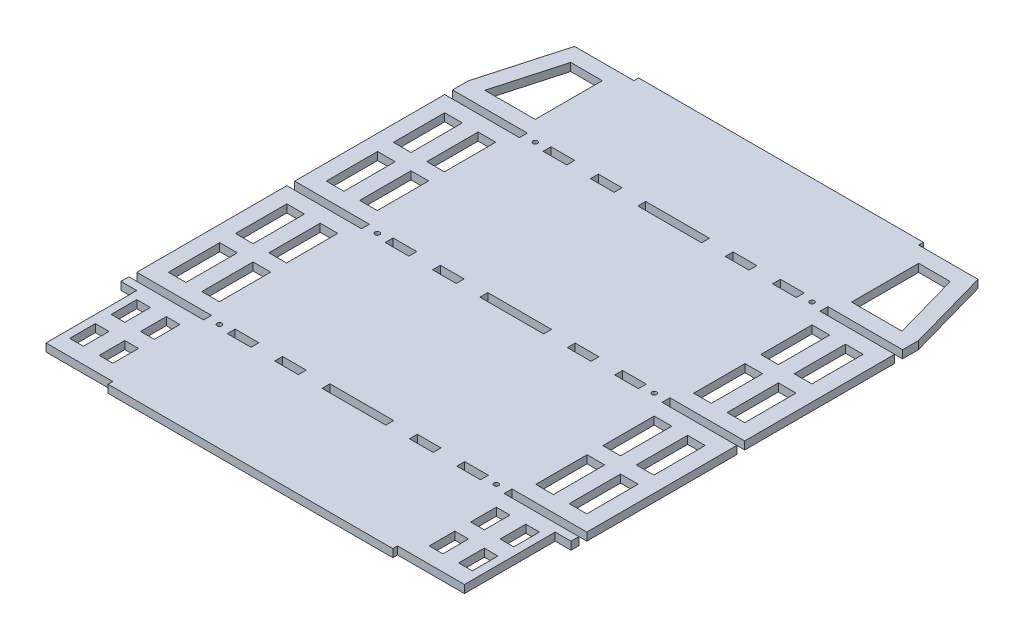
SolidWorks part; units mm, degrees
material "PMMA"
ref_plane "Front Plane" through (0, 0, 0) normal (0, 0, 1) x (1, 0, 0)
ref_plane "Top Plane" through (0, 0, 0) normal (0, 1, 0) x (1, 0, 0)
ref_plane "Right Plane" through (0, 0, 0) normal (1, 0, 0) x (0, 0, -1)
sketch "Schizzo1" plane through (0, 0, 0) normal (0, 1, 0) x (1, 0, 0)
  line L0 (-142.5, 165) -> (142.5, -165) construction
  line L1 (-142.5, 165) -> (142.5, 165)
  line L2 (-142.5, 165) -> (-142.5, -165)
  line L3 (-142.5, -165) -> (142.5, -165)
  line L4 (142.5, 165) -> (142.5, -165)
  point P4 (0, 0)
  dimension "D1" = 330
  dimension "D2" = 285
extrude "Estrusione-Estrusione1" add sketch "Schizzo1" along normal blind 5
sketch "Schizzo3" plane through (0, 0, 0) normal (0, 1, 0) x (1, 0, 0)
  line L0 (-142.5, 0) -> (142.5, 0) construction
  line L1 (-142.5, 165) -> (-142.5, -165) construction
  line L2 (-20.18, -102.5) -> (20.18, -102.5)
  line L3 (0, 165) -> (0, -165) construction
  line L4 (142.5, 165) -> (-142.5, 165) construction
  line L5 (-142.5, -165) -> (142.5, -165) construction
  line L6 (-50.18, -2.5) -> (-35.18, -2.5)
  line L7 (-80.18, 2.5) -> (-65.18, 2.5)
  line L8 (-80.18, 2.5) -> (-80.18, -2.5)
  line L9 (-80.18, -2.5) -> (-65.18, -2.5)
  line L10 (-65.18, 2.5) -> (-65.18, -2.5)
  line L11 (-35.18, 2.5) -> (-35.18, -2.5)
  line L12 (-50.18, 2.5) -> (-35.18, 2.5)
  line L13 (-50.18, 2.5) -> (-50.18, -2.5)
  line L14 (80.18, 2.5) -> (80.18, -2.5)
  line L15 (80.18, 2.5) -> (65.18, 2.5)
  line L16 (65.18, 2.5) -> (65.18, -2.5)
  line L17 (80.18, -2.5) -> (65.18, -2.5)
  line L18 (50.18, 2.5) -> (50.18, -2.5)
  line L19 (50.18, 2.5) -> (35.18, 2.5)
  line L20 (35.18, 2.5) -> (35.18, -2.5)
  line L21 (50.18, -2.5) -> (35.18, -2.5)
  line L22 (-80.18, 97.5) -> (-65.18, 97.5)
  line L23 (-65.18, 102.5) -> (-65.18, 97.5)
  line L24 (-80.18, 102.5) -> (-65.18, 102.5)
  line L25 (-80.18, 102.5) -> (-80.18, 97.5)
  line L26 (-50.18, 97.5) -> (-35.18, 97.5)
  line L27 (-35.18, 102.5) -> (-35.18, 97.5)
  line L28 (-50.18, 102.5) -> (-35.18, 102.5)
  line L29 (-50.18, 102.5) -> (-50.18, 97.5)
  line L30 (-80.18, -102.5) -> (-65.18, -102.5)
  line L31 (-65.18, -97.5) -> (-65.18, -102.5)
  line L32 (-80.18, -97.5) -> (-65.18, -97.5)
  line L33 (-80.18, -97.5) -> (-80.18, -102.5)
  line L34 (-50.18, -102.5) -> (-35.18, -102.5)
  line L35 (-35.18, -97.5) -> (-35.18, -102.5)
  line L36 (-50.18, -97.5) -> (-35.18, -97.5)
  line L37 (-50.18, -97.5) -> (-50.18, -102.5)
  line L38 (50.18, 102.5) -> (50.18, 97.5)
  line L39 (50.18, 102.5) -> (35.18, 102.5)
  line L40 (35.18, 102.5) -> (35.18, 97.5)
  line L41 (50.18, 97.5) -> (35.18, 97.5)
  line L42 (80.18, 102.5) -> (80.18, 97.5)
  line L43 (80.18, 102.5) -> (65.18, 102.5)
  line L44 (65.18, 102.5) -> (65.18, 97.5)
  line L45 (80.18, 97.5) -> (65.18, 97.5)
  line L46 (50.18, -97.5) -> (50.18, -102.5)
  line L47 (50.18, -97.5) -> (35.18, -97.5)
  line L48 (35.18, -97.5) -> (35.18, -102.5)
  line L49 (50.18, -102.5) -> (35.18, -102.5)
  line L50 (80.18, -97.5) -> (80.18, -102.5)
  line L51 (80.18, -97.5) -> (65.18, -97.5)
  line L52 (65.18, -97.5) -> (65.18, -102.5)
  line L53 (80.18, -102.5) -> (65.18, -102.5)
  line L54 (142.5, -165) -> (142.5, 165) construction
  line L55 (-142.5, 97.5) -> (-95.18, 97.5)
  line L56 (-20.18, 2.5) -> (20.18, 2.5)
  line L57 (-20.18, 2.5) -> (-20.18, -2.5)
  line L58 (-20.18, -2.5) -> (20.18, -2.5)
  line L59 (20.18, 2.5) -> (20.18, -2.5)
  line L60 (20.18, -97.5) -> (20.18, -102.5)
  line L61 (-20.18, -97.5) -> (20.18, -97.5)
  line L62 (-20.18, -97.5) -> (-20.18, -102.5)
  line L63 (0, 65) -> (0, -265) construction
  line L64 (-20.18, 97.5) -> (20.18, 97.5)
  line L65 (20.18, 102.5) -> (20.18, 97.5)
  line L66 (-20.18, 102.5) -> (20.18, 102.5)
  line L67 (-20.18, 102.5) -> (-20.18, 97.5)
  line L68 (-142.5, 2.5) -> (-95.18, 2.5)
  line L69 (-142.5, 2.5) -> (-142.5, -2.5)
  line L70 (-142.5, -2.5) -> (-95.18, -2.5)
  line L71 (-95.18, 2.5) -> (-95.18, -2.5)
  line L72 (-95.18, 102.5) -> (-95.18, 97.5)
  line L73 (-142.5, 102.5) -> (-95.18, 102.5)
  line L74 (-142.5, 102.5) -> (-142.5, 97.5)
  line L75 (-142.5, -97.5) -> (-95.18, -97.5)
  line L76 (-95.18, -97.5) -> (-95.18, -102.5)
  line L77 (-142.5, -102.5) -> (-95.18, -102.5)
  line L78 (-142.5, -97.5) -> (-142.5, -102.5)
  line L79 (142.5, -97.5) -> (142.5, -102.5)
  line L80 (142.5, -102.5) -> (95.18, -102.5)
  line L81 (95.18, -97.5) -> (95.18, -102.5)
  line L82 (142.5, -97.5) -> (95.18, -97.5)
  line L83 (142.5, 102.5) -> (142.5, 97.5)
  line L84 (142.5, 102.5) -> (95.18, 102.5)
  line L85 (95.18, 102.5) -> (95.18, 97.5)
  line L86 (142.5, 97.5) -> (95.18, 97.5)
  line L87 (142.5, 2.5) -> (142.5, -2.5)
  line L88 (142.5, 2.5) -> (95.18, 2.5)
  line L89 (95.18, 2.5) -> (95.18, -2.5)
  line L90 (142.5, -2.5) -> (95.18, -2.5)
  circle A0 centre (-87.68, 0) radius 1.5
  circle A1 centre (87.68, 0) radius 1.5
  circle A2 centre (-87.68, 100) radius 1.5
  circle A3 centre (-87.68, -100) radius 1.5
  circle A4 centre (87.68, -100) radius 1.5
  circle A5 centre (87.68, 100) radius 1.5
  circle A8 centre (-5.0427, -204.0432) radius 1.5
  point P81 (-20.18, 0)
  point P82 (0, 2.5)
  point P84 (-65.18, 0)
  point P96 (-142.5, 0)
  dimension "D7" = 3
  dimension "D1" = 15
  dimension "D3" = 5
  dimension "D10" = 5
  dimension "D11" = 40.36
  dimension "D14" = 7.5
  dimension "D16" = 47.32
  dimension "D2" = 62.32
  dimension "D15" = 107.32
  dimension "D4" = 2
  dimension "D5" = 2
  dimension "D6" = 2
  dimension "D8" = 2
  dimension "D9" = 2
  dimension "D12" = 2
  dimension "D13" = 2
  dimension "D17" = 2
  dimension "D18" = 2
extrude "Taglio-Estrusione1" cut sketch "Schizzo3" along direction (0, 1, 0) on the side of the normal through all
sketch "Schizzo4" plane through (0, 0, 165) normal (0, 0, 1) x (1, 0, 0)
  line L0 (-142.5, 5) -> (142.5, 5) construction
  line L1 (-90.17, 5) -> (90.17, 5)
  line L2 (-90.17, 5) -> (-90.17, 0)
  line L3 (-90.17, 0) -> (90.17, 0)
  line L4 (90.17, 5) -> (90.17, 0)
  line L5 (-142.5, 0) -> (142.5, 0) construction
  line L6 (-142.5, 5) -> (-142.5, 0) construction
  point P4 (0, 5)
  point P7 (0, 5)
  point P10 (-142.5, 2.5)
  dimension "D1" = 52.33
extrude "Estrusione-Estrusione2" add sketch "Schizzo4" along normal blind 3
sketch "Schizzo5" plane through (0, 0, -165) normal (0, 0, -1) x (-1, 0, 0)
  line L0 (-142.5, 5) -> (142.5, 5) construction
  line L1 (-90.18, 5) -> (90.18, 5)
  line L2 (-90.18, 5) -> (-90.18, 0)
  line L3 (-90.18, 0) -> (90.18, 0)
  line L4 (90.18, 5) -> (90.18, 0)
  line L5 (-142.5, 0) -> (142.5, 0) construction
  line L6 (-142.5, 5) -> (-142.5, 0) construction
  point P4 (0, 5)
  point P7 (0, 5)
  dimension "D1" = 52.32
extrude "Estrusione-Estrusione3" add sketch "Schizzo5" along normal blind 3
sketch "Schizzo6" plane through (0, 0, 0) normal (0, 1, 0) x (1, 0, 0)
  line L0 (-142.5, 165) -> (-127.7589, 165)
  line L1 (-90.18, 165) -> (-142.5, 165) construction
  line L2 (-127.7589, 165) -> (-142.5, 112.5)
  line L3 (-142.5, 165) -> (-142.5, 102.5) construction
  line L4 (-142.5, 112.5) -> (-142.5, 165)
  line L5 (-95.18, 102.5) -> (-142.5, 102.5) construction
  line L6 (-132.1133, 112.5) -> (-100.18, 112.5)
  line L7 (-100.18, 112.5) -> (-100.18, 155)
  line L8 (-100.18, 155) -> (-120.18, 155)
  line L9 (-120.18, 155) -> (-132.1133, 112.5)
  line L10 (108.84, -138.75) -> (108.84, -155)
  line L11 (108.84, -155) -> (100.18, -155)
  line L12 (100.18, -138.75) -> (100.18, -155)
  line L13 (108.84, -138.75) -> (100.18, -138.75)
  line L14 (-95.18, 97.5) -> (-95.18, 102.5) construction
  line L15 (-90.18, 168) -> (-90.18, 165) construction
  line L16 (0, 168) -> (0, -168) construction
  line L17 (-90.18, 168) -> (90.18, 168) construction
  line L18 (90.17, -168) -> (-90.17, -168) construction
  line L19 (132.1133, 112.5) -> (100.18, 112.5)
  line L20 (120.18, 155) -> (132.1133, 112.5)
  line L21 (100.18, 155) -> (120.18, 155)
  line L22 (100.18, 112.5) -> (100.18, 155)
  line L23 (142.5, 165) -> (127.7589, 165)
  line L24 (142.5, 112.5) -> (142.5, 165)
  line L25 (127.7589, 165) -> (142.5, 112.5)
  line L26 (-142.5, -102.5) -> (-95.18, -102.5) construction
  line L27 (-127.5, -112.5) -> (-118.84, -112.5)
  line L28 (-127.5, -112.5) -> (-127.5, -128.75)
  line L29 (-127.5, -128.75) -> (-118.84, -128.75)
  line L30 (-118.84, -112.5) -> (-118.84, -128.75)
  line L31 (-142.5, -102.5) -> (-142.5, -165) construction
  line L32 (-108.84, -112.5) -> (-100.18, -112.5)
  line L33 (-108.84, -112.5) -> (-108.84, -128.75)
  line L34 (-108.84, -128.75) -> (-100.18, -128.75)
  line L35 (-100.18, -112.5) -> (-100.18, -128.75)
  line L36 (-95.18, -102.5) -> (-95.18, -97.5) construction
  line L37 (-127.5, -138.75) -> (-118.84, -138.75)
  line L38 (-127.5, -138.75) -> (-127.5, -155)
  line L39 (-127.5, -155) -> (-118.84, -155)
  line L40 (-118.84, -138.75) -> (-118.84, -155)
  line L41 (-108.84, -138.75) -> (-100.18, -138.75)
  line L42 (-108.84, -138.75) -> (-108.84, -155)
  line L43 (-108.84, -155) -> (-100.18, -155)
  line L44 (-100.18, -138.75) -> (-100.18, -155)
  line L45 (-142.5, -165) -> (-90.17, -165) construction
  line L46 (127.5, -138.75) -> (127.5, -155)
  line L47 (127.5, -155) -> (118.84, -155)
  line L48 (118.84, -138.75) -> (118.84, -155)
  line L49 (127.5, -138.75) -> (118.84, -138.75)
  line L50 (108.84, -112.5) -> (108.84, -128.75)
  line L51 (108.84, -112.5) -> (100.18, -112.5)
  line L52 (100.18, -112.5) -> (100.18, -128.75)
  line L53 (108.84, -128.75) -> (100.18, -128.75)
  line L54 (127.5, -112.5) -> (127.5, -128.75)
  line L55 (127.5, -112.5) -> (118.84, -112.5)
  line L56 (118.84, -112.5) -> (118.84, -128.75)
  line L57 (127.5, -128.75) -> (118.84, -128.75)
  line L58 (-132.5, -12.5) -> (-121.34, -12.5)
  line L59 (-132.5, -12.5) -> (-132.5, -45)
  line L60 (-132.5, -45) -> (-121.34, -45)
  line L61 (-121.34, -12.5) -> (-121.34, -45)
  line L62 (-111.34, -12.5) -> (-100.18, -12.5)
  line L63 (-111.34, -12.5) -> (-111.34, -45)
  line L64 (-111.34, -45) -> (-100.18, -45)
  line L65 (-100.18, -12.5) -> (-100.18, -45)
  line L66 (-132.5, -55) -> (-121.34, -55)
  line L67 (-132.5, -55) -> (-132.5, -87.5)
  line L68 (-132.5, -87.5) -> (-121.34, -87.5)
  line L69 (-121.34, -55) -> (-121.34, -87.5)
  line L70 (-111.34, -55) -> (-100.18, -55)
  line L71 (-111.34, -55) -> (-111.34, -87.5)
  line L72 (-111.34, -87.5) -> (-100.18, -87.5)
  line L73 (-100.18, -55) -> (-100.18, -87.5)
  line L74 (-142.5, -2.5) -> (-142.5, -97.5) construction
  line L75 (-142.5, -2.5) -> (-95.18, -2.5) construction
  line L76 (-95.18, -2.5) -> (-95.18, 2.5) construction
  line L77 (-95.18, -97.5) -> (-142.5, -97.5) construction
  line L78 (111.34, -55) -> (100.18, -55)
  line L79 (111.34, -55) -> (111.34, -87.5)
  line L80 (111.34, -87.5) -> (100.18, -87.5)
  line L81 (100.18, -55) -> (100.18, -87.5)
  line L82 (132.5, -55) -> (121.34, -55)
  line L83 (132.5, -55) -> (132.5, -87.5)
  line L84 (132.5, -87.5) -> (121.34, -87.5)
  line L85 (121.34, -55) -> (121.34, -87.5)
  line L86 (111.34, -12.5) -> (100.18, -12.5)
  line L87 (111.34, -12.5) -> (111.34, -45)
  line L88 (111.34, -45) -> (100.18, -45)
  line L89 (100.18, -12.5) -> (100.18, -45)
  line L90 (132.5, -12.5) -> (121.34, -12.5)
  line L91 (132.5, -12.5) -> (132.5, -45)
  line L92 (132.5, -45) -> (121.34, -45)
  line L93 (121.34, -12.5) -> (121.34, -45)
  line L94 (-95.18, 0) -> (95.18, 0) construction
  line L95 (95.18, 2.5) -> (95.18, -2.5) construction
  line L96 (111.34, 55) -> (100.18, 55)
  line L97 (100.18, 55) -> (100.18, 87.5)
  line L98 (111.34, 87.5) -> (100.18, 87.5)
  line L99 (111.34, 55) -> (111.34, 87.5)
  line L100 (132.5, 55) -> (121.34, 55)
  line L101 (121.34, 55) -> (121.34, 87.5)
  line L102 (132.5, 87.5) -> (121.34, 87.5)
  line L103 (132.5, 55) -> (132.5, 87.5)
  line L104 (132.5, 12.5) -> (121.34, 12.5)
  line L105 (121.34, 12.5) -> (121.34, 45)
  line L106 (132.5, 45) -> (121.34, 45)
  line L107 (132.5, 12.5) -> (132.5, 45)
  line L108 (111.34, 12.5) -> (100.18, 12.5)
  line L109 (111.34, 12.5) -> (111.34, 45)
  line L110 (111.34, 45) -> (100.18, 45)
  line L111 (100.18, 12.5) -> (100.18, 45)
  line L112 (-132.5, 55) -> (-121.34, 55)
  line L113 (-132.5, 55) -> (-132.5, 87.5)
  line L114 (-132.5, 87.5) -> (-121.34, 87.5)
  line L115 (-121.34, 55) -> (-121.34, 87.5)
  line L116 (-111.34, 55) -> (-100.18, 55)
  line L117 (-111.34, 55) -> (-111.34, 87.5)
  line L118 (-111.34, 87.5) -> (-100.18, 87.5)
  line L119 (-100.18, 55) -> (-100.18, 87.5)
  line L120 (-111.34, 12.5) -> (-100.18, 12.5)
  line L121 (-111.34, 12.5) -> (-111.34, 45)
  line L122 (-111.34, 45) -> (-100.18, 45)
  line L123 (-100.18, 12.5) -> (-100.18, 45)
  line L124 (-132.5, 12.5) -> (-121.34, 12.5)
  line L125 (-132.5, 12.5) -> (-132.5, 45)
  line L126 (-132.5, 45) -> (-121.34, 45)
  line L127 (-121.34, 12.5) -> (-121.34, 45)
  line L128 (142.5, -107.5) -> (132.5, -107.5)
  line L129 (-142.5, -107.5) -> (-132.5, -107.5)
  line L130 (-142.5, -107.5) -> (-142.5, -165)
  line L131 (-142.5, -165) -> (-132.5, -165)
  line L132 (-132.5, -107.5) -> (-132.5, -165)
  line L133 (142.5, -107.5) -> (142.5, -165)
  line L134 (142.5, -165) -> (132.5, -165)
  line L135 (132.5, -107.5) -> (132.5, -165)
  point P13 (-95.18, 100)
  point P45 (-95.18, -100)
  dimension "D1" = 10
  dimension "D2" = 5
  dimension "D3" = 20
  dimension "D4" = 10
  dimension "D5" = 10
  dimension "D6" = 10
  dimension "D7" = 10
  dimension "D8" = 15
  dimension "D9" = 10
  dimension "D10" = 5
  dimension "D11" = 10
  dimension "D12" = 10
  dimension "D13" = 10
  dimension "D14" = 10
  dimension "D15" = 10
  dimension "D16" = 10
  dimension "D17" = 5
  dimension "D18" = 10
  dimension "D19" = 10
  dimension "D20" = 5
extrude "Taglio-Estrusione2" cut sketch "Schizzo6" along direction (0, 1, 0) on the side of the normal through all
equation "\"Thickness5\"= 5"
equation "\"D1@Estrusione-Estrusione1\"=\"Thickness5\""
equation "\"D3@Schizzo3\"=\"Thickness5\""
equation "\"D10@Schizzo3\"=\"Thickness5\""
equation "\"Thickness3\"= 3"
equation "\"D1@Estrusione-Estrusione2\"=\"Thickness3\""
equation "\"D1@Estrusione-Estrusione3\"=\"Thickness3\""
